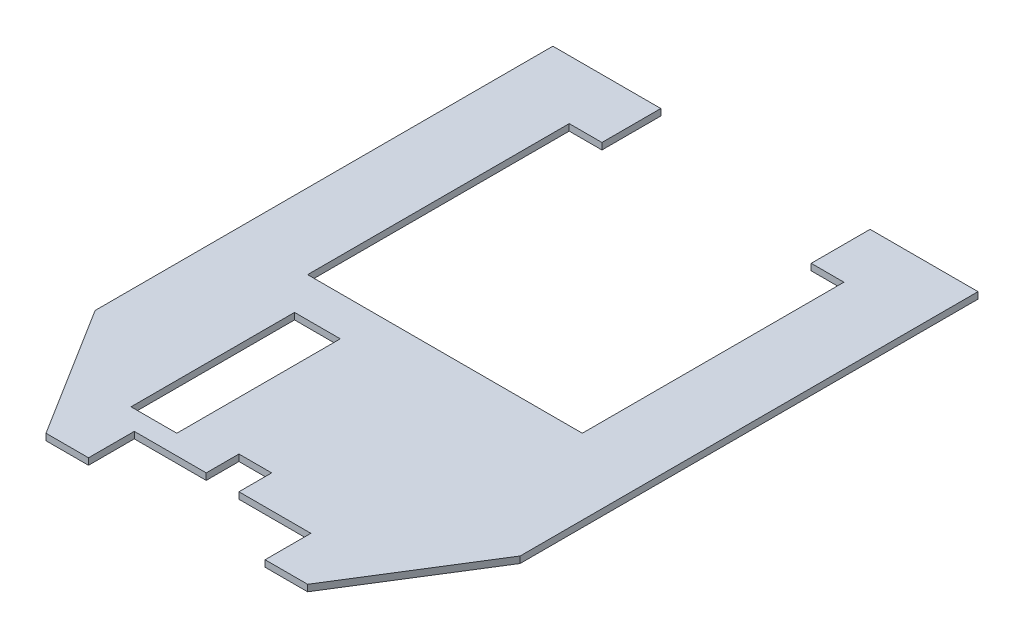
SolidWorks part; units mm, degrees
material "1060 Alloy"
ref_plane "Front Plane" through (0, 0, 0) normal (0, 0, 1) x (1, 0, 0)
ref_plane "Top Plane" through (0, 0, 0) normal (0, 1, 0) x (1, 0, 0)
ref_plane "Right Plane" through (0, 0, 0) normal (1, 0, 0) x (0, 0, -1)
sketch "Sketch1" plane through (0, 0, 0) normal (0, 1, 0) x (1, 0, 0)
  line L0 (-20, -20) -> (-13.5, -20)
  line L1 (20, -20) -> (32.5, 0)
  line L2 (32.5, 0) -> (32.5, 70)
  line L3 (32.5, 70) -> (16, 70)
  line L4 (-32.5, 70) -> (-32.5, 0)
  line L5 (-32.5, 0) -> (-20, -20)
  line L6 (-13.5, -20) -> (-13.5, -13)
  line L7 (21, 61) -> (16, 61)
  line L8 (21, 61) -> (21, 21)
  line L9 (21, 21) -> (-21, 21)
  line L10 (-21, 61) -> (-21, 21)
  line L11 (-10, -10) -> (-17, -10)
  line L12 (-10, -10) -> (-10, 15)
  line L13 (-10, 15) -> (-17, 15)
  line L14 (-17, -10) -> (-17, 15)
  line L15 (16, 61) -> (16, 70)
  line L16 (-16, 61) -> (-16, 70)
  line L17 (-13.5, -13) -> (-2.5, -13)
  line L18 (-2.5, -13) -> (-2.5, -8)
  line L19 (-2.5, -8) -> (2.5, -8)
  line L20 (2.5, -8) -> (2.5, -13)
  line L21 (2.5, -13) -> (13.5, -13)
  line L22 (13.5, -13) -> (13.5, -20)
  line L23 (13.5, -20) -> (20, -20)
  line L24 (-16, 61) -> (-21, 61)
  line L25 (-16, 70) -> (-32.5, 70)
  point P7 (0, -8)
  point P13 (0, 21)
  dimension "D1" = 40
  dimension "D2" = 65
  dimension "D3" = 20
  dimension "D4" = 90
  dimension "D5" = 42
  dimension "D6" = 40
  dimension "D7" = 7
  dimension "D8" = 25
  dimension "D9" = 10
  dimension "D10" = 3
  dimension "D11" = 41
  dimension "D12" = 6.5
  dimension "D13" = 5
  dimension "D14" = 6.5
  dimension "D15" = 7
  dimension "D16" = 5
  dimension "D17" = 5
  dimension "D18" = 5
  dimension "D19" = 16.5
extrude "Extrude1" add sketch "Sketch1" along normal blind 1
